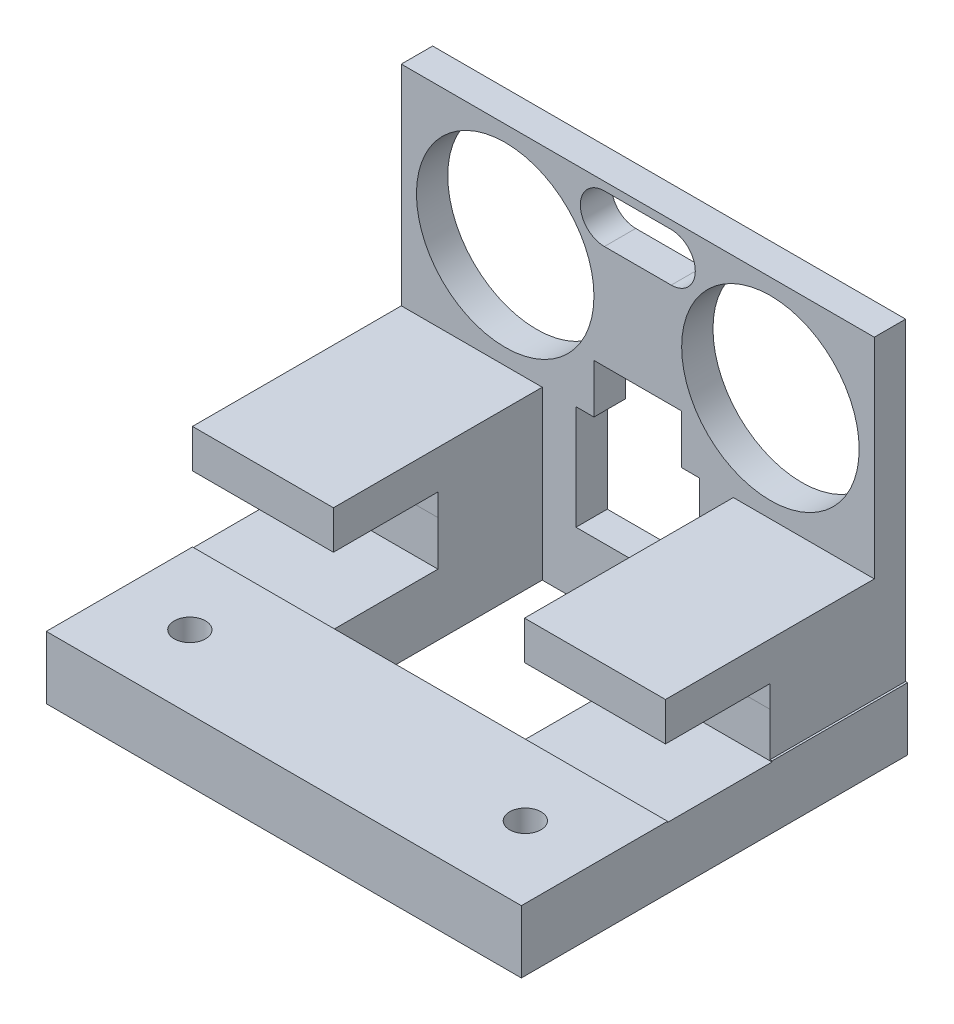
SolidWorks part; units mm, degrees
ref_plane "Front Plane" through (0, 0, 0) normal (0, 0, 1) x (1, 0, 0)
ref_plane "Top Plane" through (0, 0, 0) normal (0, 1, 0) x (1, 0, 0)
ref_plane "Right Plane" through (0, 0, 0) normal (1, 0, 0) x (0, 0, -1)
sketch "Sketch1" plane through (0, 0, 0) normal (0, 0, 1) x (1, 0, 0)
  line L1 (0, 0) -> (45.3, 0)
  line L2 (0, 0) -> (0, 20.05)
  line L3 (0, 20.05) -> (45.3, 20.05)
  line L4 (45.3, 0) -> (45.3, 20.05)
  dimension "D1" = 45.3
  dimension "D2" = 20.05
extrude "Boss-Extrude1" add sketch "Sketch1" along normal blind 3
sketch "Sketch2" plane through (0, 0, 3) normal (0, 0, 1) x (1, 0, 0)
  line L0 (22.65, 20.05) -> (22.65, 0) construction
  line L1 (45.3, 20.05) -> (0, 20.05) construction
  line L2 (0, 0) -> (45.3, 0) construction
  line L3 (22.65, 0) -> (0, 0) construction
  line L4 (0, 0) -> (0, 20.05) construction
  line L5 (22.65, 20.05) -> (9.95, 20.05) construction
  line L6 (9.95, 20.05) -> (9.95, 17.85) construction
  line L7 (22.65, 10.025) -> (0, 10.025) construction
  line L8 (0.6992, 10.025) -> (0, 10.025) construction
  line L9 (9.95, 17.85) -> (9.95, 0) construction
  line L10 (1.45, 10.025) -> (1.45, 0) construction
  line L11 (9.95, 10.025) -> (18.45, 10.025) construction
  line L12 (0, 20.05) -> (0.15, 20.05) construction
  line L13 (22.65, 20.05) -> (22.65, 19.25) construction
  line L14 (22.65, 19.25) -> (25.85, 19.25) construction
  line L15 (25.85, 19.25) -> (25.85, 14.65) construction
  line L16 (25.85, 14.65) -> (19.45, 14.65) construction
  line L17 (19.45, 14.65) -> (19.45, 19.25) construction
  line L18 (19.45, 19.25) -> (22.65, 19.25) construction
  line L19 (22.65, 19.25) -> (22.65, 14.65) construction
  line L20 (22.65, 14.65) -> (22.65, 16.95) construction
  line L21 (22.65, 16.95) -> (25.85, 16.95) construction
  line L22 (25.85, 16.95) -> (19.45, 16.95) construction
  line L23 (19.45, 16.95) -> (25.85, 16.95) construction
  line L24 (19.45, 19.2556) -> (25.85, 19.2556)
  line L25 (19.45, 14.6444) -> (25.85, 14.6444)
  line L26 (19.45, 16.95) -> (17.1444, 16.95) construction
  line L27 (17.1444, 16.95) -> (28.1556, 16.95) construction
  circle A1 centre (9.95, 10.025) radius 8.5
  circle A2 centre (35.35, 10.025) radius 8.5
  arc A3 (19.45, 19.2556) -> (19.45, 14.6444) centre (19.45, 16.95) ccw
  arc A4 (25.85, 14.6444) -> (25.85, 19.2556) centre (25.85, 16.95) ccw
  point P34 (22.65, 16.95)
  dimension "D4" = 17
  dimension "D2" = 2.2
  dimension "D3" = 0.6992
  dimension "D5" = 1.45
  dimension "D7" = 0.15
  dimension "D10" = 0.8
  dimension "D11" = 4.6
extrude "Cut-Extrude1" cut sketch "Sketch2" against normal through all
sketch "Sketch3" plane through (0, 0, 3) normal (0, 0, 1) x (1, 0, 0)
  line L0 (18.45, 10.025) -> (18.45, 0) construction
  line L1 (0, 0) -> (45.3, 0) construction
  line L2 (18.45, 0) -> (18.45, 10.025) construction
  line L3 (18.45, 10.025) -> (26.85, 10.025) construction
  line L4 (26.85, 10.025) -> (26.85, 0) construction
  line L5 (26.85, 0) -> (18.45, 0) construction
  line L6 (18.45, 0) -> (18.45, 4.7) construction
  line L7 (18.45, 4.7) -> (26.85, 4.7) construction
  line L9 (18.45, 4.7) -> (26.85, 4.7)
  line L10 (18.45, 4.7) -> (18.45, 0)
  line L11 (18.45, 0) -> (26.85, 0)
  line L12 (26.85, 4.7) -> (26.85, 0)
  circle A0 centre (9.95, 10.025) radius 8.5 construction
  circle A1 centre (35.35, 10.025) radius 8.5 construction
extrude "Cut-Extrude2" cut sketch "Sketch3" against normal blind 1
sketch "Sketch10" plane through (0, 0, 0) normal (0, -1, 0) x (1, 0, 0)
  line L0 (0, 0) -> (45.3, 0) construction
  line L1 (0, 3) -> (16.7284, 3)
  line L2 (0, 3) -> (0, 0)
  line L3 (0, 0) -> (16.7284, 0)
  line L4 (16.7284, 3) -> (16.7284, 0)
  line L5 (22.65, 0) -> (22.65, 7.4853) construction
  line L6 (45.3, 0) -> (28.5716, 0)
  line L7 (28.5716, 3) -> (28.5716, 0)
  line L8 (45.3, 3) -> (28.5716, 3)
  line L9 (45.3, 3) -> (45.3, 0)
extrude "Boss-Extrude8" add sketch "Sketch10" along normal blind 10
sketch "Sketch11" plane through (0, 0, 3) normal (0, 0, 1) x (1, 0, 0)
  line L0 (22.65, 0) -> (22.65, -8.4576) construction
  line L5 (18.45, 0) -> (26.85, 0) construction
  line L10 (16.7284, -10) -> (0, -10) construction
  line L11 (0, 0) -> (13.5, 0)
  line L12 (0, 0) -> (0, -10)
  line L13 (0, -10) -> (13.5, -10)
  line L14 (13.5, 0) -> (13.5, -10)
  line L15 (45.3, -10) -> (31.8, -10)
  line L16 (31.8, 0) -> (31.8, -10)
  line L17 (45.3, 0) -> (31.8, 0)
  line L18 (45.3, 0) -> (45.3, -10)
  dimension "D1" = 13.5
extrude "Boss-Extrude9" add sketch "Sketch11" along normal blind 20
sketch "Sketch12" plane through (0, 0, 23) normal (0, 0, 1) x (1, 0, 0)
  line L0 (0, -3.69) -> (45.3, -3.69) construction
  line L1 (0, 0) -> (0, -10) construction
  line L2 (45.3, -10) -> (45.3, 0) construction
  line L3 (13.5, -10) -> (13.5, 0) construction
  line L4 (0, -3.69) -> (13.5, -3.69)
  line L5 (0, -3.69) -> (0, -5.81)
  line L6 (0, -5.81) -> (13.5, -5.81)
  line L7 (13.5, -3.69) -> (13.5, -5.81)
  line L8 (22.65, -3.69) -> (22.65, -0.877) construction
  line L9 (45.3, -5.81) -> (31.8, -5.81)
  line L10 (31.8, -3.69) -> (31.8, -5.81)
  line L11 (45.3, -3.69) -> (31.8, -3.69)
  line L12 (45.3, -3.69) -> (45.3, -5.81)
  dimension "D1" = 45.3
  dimension "D2" = 2.12
extrude "Cut-Extrude3" cut sketch "Sketch12" against normal blind 10
sketch "Sketch13" plane through (0, -10, 0) normal (0, -1, 0) x (1, 0, 0)
  line L0 (13.5, 23) -> (13.5, 3) construction
  line L1 (0, 0) -> (13.5, 0)
  line L2 (0, 0) -> (0, 4)
  line L3 (0, 4) -> (13.5, 4)
  line L4 (13.5, 0) -> (13.5, 4)
  dimension "D1" = 4
extrude "Boss-Extrude10" add sketch "Sketch13" along normal blind 6
sketch "Sketch14" plane through (13.5, 0, 0) normal (1, 0, 0) x (0, 0, -1)
  line L0 (0, -16) -> (0, -10) construction
  line L1 (-4, -16) -> (0, -16)
  line L2 (-4, -16) -> (-4, -13)
  line L3 (-4, -13) -> (0, -13)
  line L4 (0, -16) -> (0, -13)
  dimension "D1" = 3
extrude "Boss-Extrude11" add sketch "Sketch14" along normal blind 32
sketch "Sketch15" plane through (0, -13, 0) normal (0, 1, 0) x (1, 0, 0)
  line L1 (13.5, 0) -> (45.5, 0)
  line L2 (13.5, 0) -> (13.5, -4)
  line L3 (13.5, -4) -> (45.5, -4)
  line L4 (45.5, 0) -> (45.5, -4)
extrude "Boss-Extrude12" add sketch "Sketch15" along normal blind 3
sketch "Sketch16" plane through (0, 0, 4) normal (0, 0, 1) x (1, 0, 0)
  line L1 (0, -10) -> (45.5, -10)
  line L2 (0, -10) -> (0, -16)
  line L3 (0, -16) -> (45.5, -16)
  line L4 (45.5, -10) -> (45.5, -16)
extrude "Boss-Extrude13" add sketch "Sketch16" along normal blind 33
sketch "Sketch17" plane through (0, -10, 0) normal (0, 1, 0) x (1, 0, 0)
  line L1 (13.5, -3) -> (31.8, -3)
  line L2 (13.5, -3) -> (13.5, -23)
  line L3 (13.5, -23) -> (31.8, -23)
  line L4 (31.8, -3) -> (31.8, -23)
extrude "Cut-Extrude4" cut sketch "Sketch17" against normal through all
sketch "Sketch18" plane through (0, -10, 0) normal (0, 1, 0) x (1, 0, 0)
  line L0 (22.65, -23) -> (22.75, -37) construction
  line L1 (13.5, -23) -> (31.8, -23) construction
  line L2 (45.5, -37) -> (0, -37) construction
  line L3 (22.75, -37) -> (22.7, -30) construction
  line L4 (22.7, -30) -> (0, -30) construction
  line L5 (0, -37) -> (0, -23) construction
  line L6 (0, -30) -> (45.5, -30) construction
  line L7 (45.5, -37) -> (45.5, 0) construction
  line L8 (6.75, -23) -> (6.75, -37) construction
  line L9 (0, -23) -> (13.5, -23) construction
  line L10 (6.75, -37) -> (38.55, -23) construction
  line L11 (31.8, -23) -> (45.3, -23) construction
  line L12 (38.55, -23) -> (38.55, -37) construction
  circle A0 centre (6.75, -30) radius 1.5
  circle A1 centre (38.6484, -29.7722) radius 1.5
  dimension "D1" = 3
extrude "Cut-Extrude5" cut sketch "Sketch18" against normal through all
sketch "Sketch20" plane through (0, 0, 0) normal (-1, 0, 0) x (0, 0, 1)
  line L1 (23, -5.81) -> (12.9912, -5.81)
  line L2 (23, -5.81) -> (23, -10.0944)
  line L3 (23, -10.0944) -> (12.9912, -10.0944)
  line L4 (12.9912, -5.81) -> (12.9912, -10.0944)
extrude "Cut-Extrude6" cut sketch "Sketch20" against normal through all
sketch "Sketch21" plane through (0, 0, 2) normal (0, 0, 1) x (1, 0, 0)
  line L1 (18.45, 4.7) -> (26.85, 4.7)
  line L2 (18.45, 4.7) -> (18.45, 0)
  line L3 (18.45, 0) -> (26.85, 0)
  line L4 (26.85, 4.7) -> (26.85, 0)
extrude "Cut-Extrude7" cut sketch "Sketch21" against normal through all
